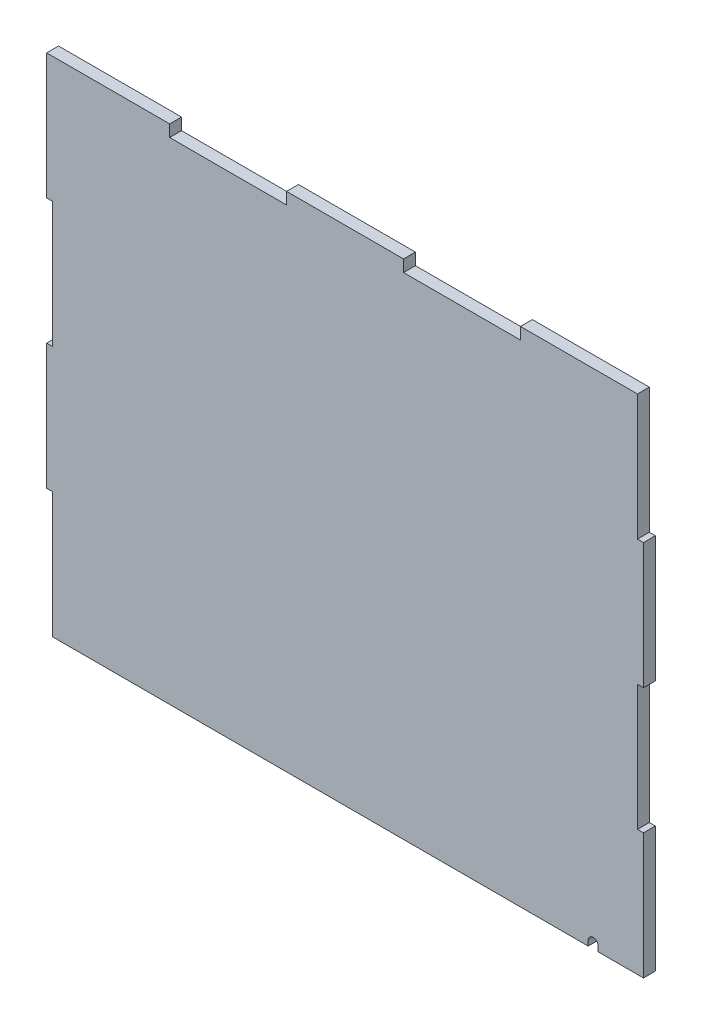
SolidWorks part; units mm, degrees
material "Acrylic (Medium-high impact)"
ref_plane "Front Plane" through (0, 0, 0) normal (0, 0, 1) x (1, 0, 0)
ref_plane "Top Plane" through (0, 0, 0) normal (0, 1, 0) x (1, 0, 0)
ref_plane "Right Plane" through (0, 0, 0) normal (1, 0, 0) x (0, 0, -1)
sketch "Sketch1" plane through (0, 0, 0) normal (0, 0, 1) x (1, 0, 0)
  line L2 (-3.048, 63.5) -> (-3.048, 127)
  line L3 (-3.048, 253.9817) -> (59.0804, 253.9817)
  line L4 (298.45, 0) -> (298.45, 63.5)
  line L7 (0, 0) -> (0, 63.5)
  line L8 (0, 63.5) -> (-3.048, 63.5)
  line L9 (0, 127) -> (-3.048, 127)
  line L10 (0, 127) -> (0, 190.5)
  line L11 (0, 190.5) -> (-3.048, 190.5)
  line L12 (-3.048, 190.5) -> (-3.048, 253.9817)
  line L13 (0, 0) -> (298.45, 0)
  line L14 (59.0804, 253.9817) -> (59.0804, 248.0127)
  line L15 (59.0804, 248.0127) -> (118.1608, 248.0127)
  line L16 (118.1608, 248.0127) -> (118.1608, 253.9817)
  line L17 (177.2412, 253.9817) -> (177.2412, 248.0127)
  line L18 (177.2412, 248.0127) -> (236.3216, 248.0127)
  line L19 (236.3216, 248.0127) -> (236.3216, 253.9817)
  line L20 (118.1608, 253.9817) -> (177.2412, 253.9817)
  line L21 (236.3216, 253.9817) -> (295.402, 253.9817)
  line L22 (298.45, 63.5) -> (295.402, 63.5)
  line L23 (295.402, 63.5) -> (295.402, 126.9817)
  line L24 (295.402, 126.9817) -> (298.45, 126.9817)
  line L25 (298.45, 190.4817) -> (295.402, 190.4817)
  line L26 (295.402, 190.4817) -> (295.402, 253.9817)
  line L29 (298.45, 126.9817) -> (298.45, 190.4817)
  dimension "D1" = 254
  dimension "D2" = 298.45
  dimension "D3" = 59.0804
  dimension "D6" = 63.5
  dimension "D7" = 3.048
  dimension "D8" = 5.969
  dimension "D10" = 3.048
extrude "Boss-Extrude1" add sketch "Sketch1" along normal blind 5.9944
sketch "Sketch2" plane through (0, 0, 5.9944) normal (0, 0, 1) x (1, 0, 0)
  line L0 (298.45, 0) -> (298.45, 63.5) construction
  line L1 (270.51, 2.54) -> (270.51, 0)
  line L2 (0, 0) -> (298.45, 0) construction
  line L3 (275.59, 2.54) -> (275.59, 0)
  line L4 (270.51, 0) -> (275.59, 0)
  arc A0 (275.59, 2.54) -> (270.51, 2.54) centre (273.05, 2.54) ccw
  dimension "D1" = 5.08
  dimension "D2" = 25.4
  dimension "D3" = 2.54
extrude "Cut-Extrude2" cut sketch "Sketch2" against normal up to next contours A0 L1 L4 L3
